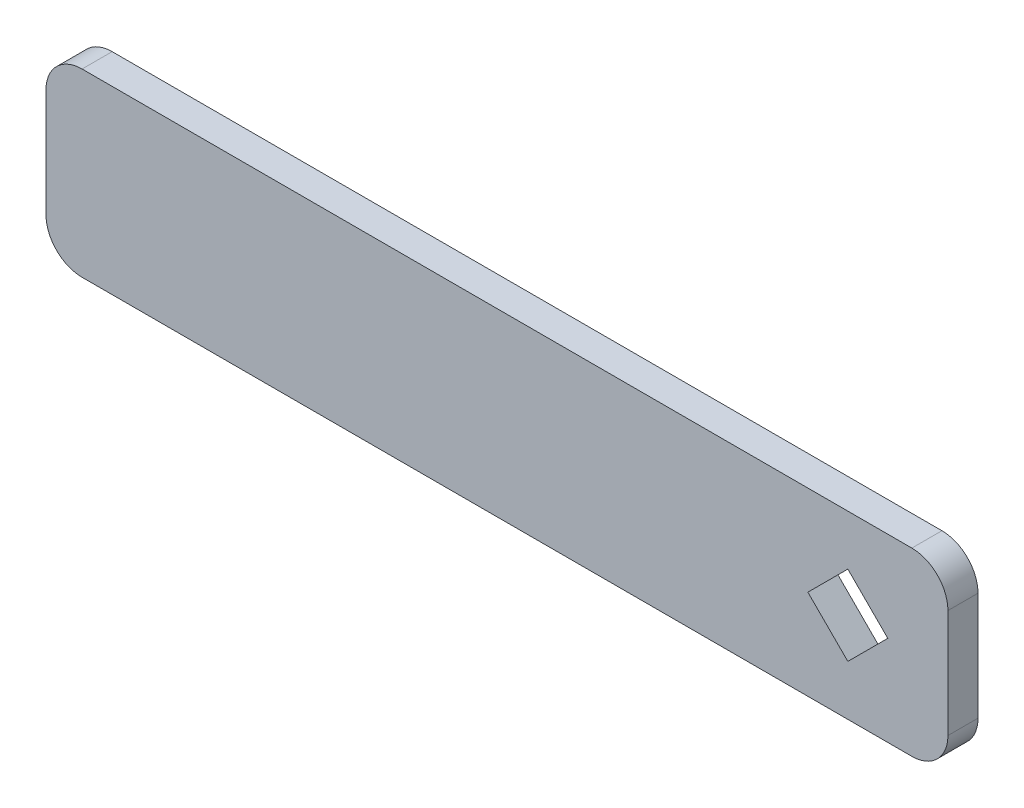
SolidWorks part; units mm, degrees
ref_plane "Plan de face" through (0, 0, 0) normal (0, 0, 1) x (1, 0, 0)
ref_plane "Plan de dessus" through (0, 0, 0) normal (0, 1, 0) x (1, 0, 0)
ref_plane "Plan de droite" through (0, 0, 0) normal (1, 0, 0) x (0, 0, -1)
sketch "Esquisse1" plane through (0, 0, 0) normal (0, 0, 1) x (1, 0, 0)
  line L1 (-75, -15) -> (75, -15)
  line L2 (-75, -15) -> (-75, 15)
  line L3 (-75, 15) -> (75, 15)
  line L4 (75, -15) -> (75, 15)
  line L5 (-75, -15) -> (75, 15) construction
  line L6 (-75, 15) -> (75, -15) construction
  line L7 (58.3532, -6.6468) -> (51.7064, 0)
  line L8 (58.3532, -6.6468) -> (65, 0)
  line L9 (65, 0) -> (58.3532, 6.6468)
  line L10 (51.7064, 0) -> (58.3532, 6.6468)
  line L11 (58.3532, -6.6468) -> (58.3532, 6.6468) construction
  line L12 (65, 0) -> (51.7064, 0) construction
  point P0 (0, 0)
  point P6 (58.3532, 0)
  dimension "D1" = 9.4
  dimension "D2" = 9.4
  dimension "D3" = 10
  dimension "D4" = 30
  dimension "D5" = 150
  dimension "D6" = 0
  dimension "D7" = 45
extrude "Boss.-Extru.1" add sketch "Esquisse1" along normal blind 5
fillet "Congé1" radius 6 4 edges at (-75, -15, 2.5) (-75, 15, 2.5) (75, -15, 2.5) (75, 15, 2.5)
